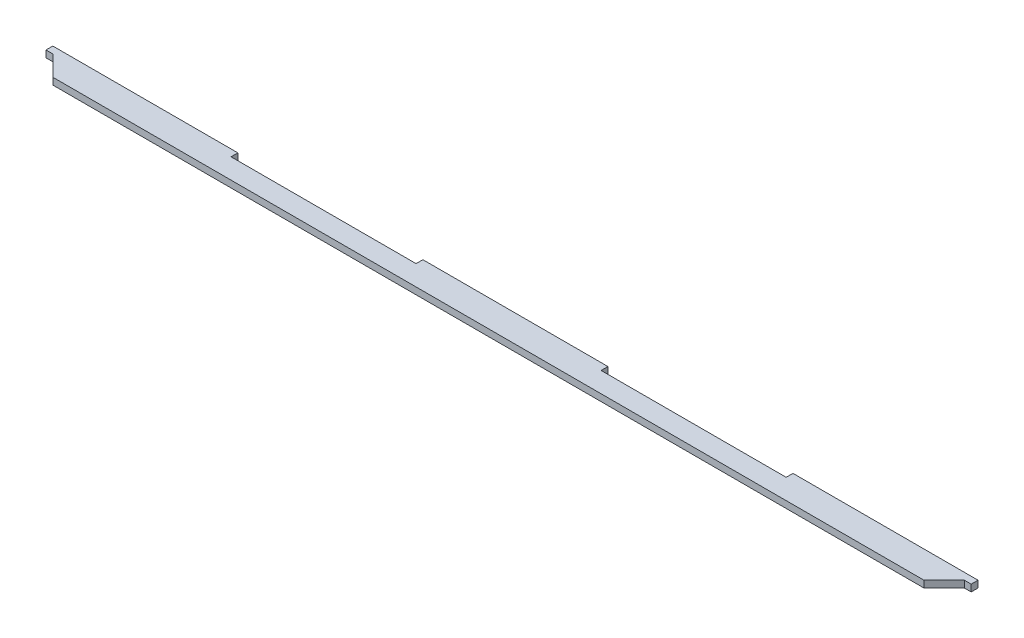
SolidWorks part; units mm, degrees
ref_plane "Front Plane" through (0, 0, 0) normal (0, 0, 1) x (1, 0, 0)
ref_plane "Top Plane" through (0, 0, 0) normal (0, 1, 0) x (1, 0, 0)
ref_plane "Right Plane" through (0, 0, 0) normal (1, 0, 0) x (0, 0, -1)
sketch "Sketch1" plane through (0, 0, 0) normal (0, 1, 0) x (1, 0, 0)
  line L0 (-183.2, 2.4056) -> (-180.5, 2.4056)
  line L1 (-183.2, 5.1056) -> (-109.92, 5.1056)
  line L2 (-183.2, 5.1056) -> (-183.2, 2.4056)
  line L3 (-172.5, -5.5944) -> (172.5, -5.5944)
  line L4 (183.2, 5.1056) -> (183.2, 2.4056)
  line L6 (-180.5, 2.4056) -> (-172.5, -5.5944)
  line L7 (180.5, 2.4056) -> (172.5, -5.5944)
  line L9 (-36.64, 5.1056) -> (36.64, 5.1056)
  line L11 (109.92, 5.1056) -> (183.2, 5.1056)
  line L12 (-109.92, 5.1056) -> (-109.92, 2.4056)
  line L13 (-36.64, 5.1056) -> (-36.64, 2.4056)
  line L14 (36.64, 5.1056) -> (36.64, 2.4056)
  line L15 (109.92, 5.1056) -> (109.92, 2.4056)
  line L16 (-109.92, 2.4056) -> (-36.64, 2.4056)
  line L17 (36.64, 2.4056) -> (109.92, 2.4056)
  line L18 (180.5, 2.4056) -> (183.2, 2.4056)
  point P0 (0, 0)
  dimension "D1" = 366.4
  dimension "D3" = 2.7
extrude "Boss-Extrude1" add sketch "Sketch1" along normal blind 2.7
